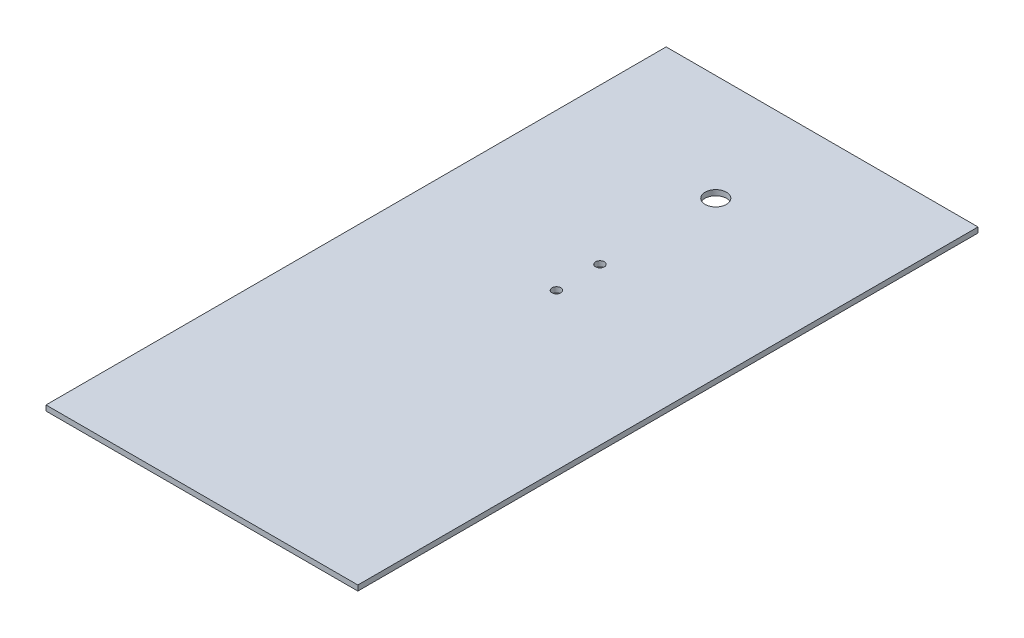
SolidWorks part; units mm, degrees
ref_plane "Front Plane" through (0, 0, 0) normal (0, 0, 1) x (1, 0, 0)
ref_plane "Top Plane" through (0, 0, 0) normal (0, 1, 0) x (1, 0, 0)
ref_plane "Right Plane" through (0, 0, 0) normal (1, 0, 0) x (0, 0, -1)
sketch "Sketch1" plane through (0, 0, 0) normal (0, 1, 0) x (1, 0, 0)
  line L1 (0, 0) -> (176, 0)
  line L2 (0, 0) -> (0, 350)
  line L3 (0, 350) -> (176, 350)
  line L4 (176, 0) -> (176, 350)
  dimension "D1" = 350
  dimension "D2" = 176
extrude "Boss-Extrude1" add sketch "Sketch1" along normal blind 3
hole_wizard "Ø5.0mm Dowel Hole1" positions "Sketch2" profile "Sketch3" hole size "Ø5.0" standard "ANSI Metric" end condition up to next
sketch "Sketch2" plane through (0, 0, 0) normal (0, -1, 0) x (-1, 0, 0)
  point P3 (-88.0169, 200.06)
  point P8 (-87.5916, 225.06)
sketch "Sketch3" plane through (88.0169, 0, -200.06) normal (1, 0, 0) x (0, 0, -1)
  line L0 (0, 0) -> (0, 3)
  line L1 (0, 3) -> (2.5, 3)
  line L2 (2.5, 3) -> (2.5, 0)
  line L5 (2.5, 0) -> (0, 0)
  line L11 (0, -6.35) -> (0, 107.95) construction
  dimension "Thru Hole Dia." = 5
  dimension "Thru Hole Depth" = 3
hole_wizard "Ø12.0mm Dowel Hole1" positions "Sketch6" profile "Sketch7" hole size "Ø12.0" standard "ANSI Metric" end condition up to next
sketch "Sketch6" plane through (0, 0, 0) normal (0, -1, 0) x (-1, 0, 0)
  point P0 (-88, 290)
sketch "Sketch7" plane through (88, 0, -290) normal (1, 0, 0) x (0, 0, -1)
  line L0 (0, 0) -> (0, 3)
  line L1 (0, 3) -> (6, 3)
  line L2 (6, 3) -> (6, 0)
  line L5 (6, 0) -> (0, 0)
  line L11 (0, -6.35) -> (0, 107.95) construction
  dimension "Thru Hole Dia." = 12
  dimension "Thru Hole Depth" = 3
sketch "Sketch10" plane through (0, 0, 0) normal (0, -1, 0) x (-1, 0, 0)
  line L0 (0, 0) -> (0, 175)
  line L1 (0, 350) -> (0, 0) construction
  line L2 (0, 175) -> (-88, 175)
sketch "Sketch12" plane through (0, 0, 0) normal (0, -1, 0) x (1, 0, 0)
  line L0 (125.0175, -130.5545) -> (137.3405, -148.3212)
  line L1 (137.3405, -148.3212) -> (125.0175, -166.0877)
  line L2 (125.0175, -166.0877) -> (112.6944, -183.8543)
  line L3 (112.6944, -183.8543) -> (89.345, -183.8589)
  line L4 (89.345, -183.8589) -> (65.9955, -183.8635)
  line L5 (65.9955, -183.8635) -> (65.9955, -187.2421)
  line L6 (65.9955, -187.2421) -> (65.9955, -190.6207)
  line L7 (65.9955, -190.6207) -> (66.5384, -190.9684)
  line L8 (62.6707, -191.0073) -> (63.1648, -190.6986)
  line L9 (63.1648, -190.6986) -> (63.169, -187.1666)
  line L10 (63.169, -187.1666) -> (63.1733, -183.6346)
  line L11 (63.1733, -183.6346) -> (50.9163, -165.9779)
  line L12 (50.9163, -165.9779) -> (38.6593, -148.3212)
  line L13 (38.6593, -148.3212) -> (50.9824, -130.5546)
  line L14 (50.9824, -130.5546) -> (63.3055, -112.788)
  line L15 (63.3055, -112.788) -> (88, -112.788)
  line L16 (88, -112.788) -> (112.6944, -112.788)
  line L17 (112.6944, -112.788) -> (125.0175, -130.5545)
  line L18 (58.6619, -161.6826) -> (67.9075, -175)
  line L19 (67.9075, -175) -> (88, -175)
  line L20 (88, -175) -> (108.0925, -175)
  line L21 (108.0925, -175) -> (117.3386, -161.6826)
  line L22 (108.8404, -122.7226) -> (108.0527, -121.5979)
  line L23 (108.0527, -121.5979) -> (87.9801, -121.6201)
  line L24 (87.9801, -121.6201) -> (67.9074, -121.6424)
  line L25 (67.9074, -121.6424) -> (58.6617, -134.9597)
  line L26 (70.518, -199.3662) -> (71.2886, -200.1403)
  line L27 (71.2886, -200.1403) -> (70.7807, -200.5699)
  line L28 (59.0664, -199.3966) -> (59.8103, -198.6687)
  line L29 (59.8103, -198.6687) -> (60.2791, -199.0503)
  line L30 (74.7643, -203.6125) -> (75.534, -204.3858)
  line L31 (75.534, -204.3858) -> (74.976, -204.8921)
  line L32 (54.138, -204.6844) -> (53.9663, -204.4929)
  line L33 (53.9663, -204.4929) -> (54.729, -203.7303)
  line L34 (54.729, -203.7303) -> (55.4916, -202.9677)
  line L35 (55.4916, -202.9677) -> (56.0106, -203.4191)
  line L36 (73.2802, -203.4581) -> (73.9945, -202.8392)
  line L37 (73.9945, -202.8392) -> (74.7643, -203.6125)
  line L38 (78.6937, -207.5419) -> (79.4376, -208.2897)
  line L39 (79.4376, -208.2897) -> (79.1768, -208.5656)
  line L40 (50.1699, -208.6539) -> (49.9988, -208.463)
  line L41 (49.9988, -208.463) -> (50.7412, -207.7168)
  spline S0 degree 3 poles (66.5384, -190.9684) (67.521, -191.5975) (68.2003, -192.821) (68.2003, -193.9618) knots 0 0 0 0 1 1 1 1
  spline S1 degree 3 poles (68.2003, -193.9618) (68.2003, -196.2879) (65.8545, -198.0438) (63.6438, -197.3723) knots 0 0 0 0 1 1 1 1
  spline S2 degree 3 poles (63.6438, -197.3723) (62.1379, -196.9149) (61.0566, -195.4901) (61.0566, -193.9632) knots 0 0 0 0 1 1 1 1
  spline S3 degree 3 poles (61.0566, -193.9632) (61.0566, -192.8424) (61.7418, -191.5877) (62.6707, -191.0073) knots 0 0 0 0 1 1 1 1
  spline S4 degree 3 poles (58.6617, -134.9597) (53.5766, -142.2843) (49.416, -148.2969) (49.4161, -148.3212) knots 0 0 0 0 1 1 1 1
  spline S5 degree 3 poles (49.4161, -148.3212) (49.4161, -148.3454) (53.5767, -154.3581) (58.6619, -161.6826) knots 0 0 0 0 1 1 1 1
  spline S6 degree 3 poles (117.3386, -161.6826) (122.424, -154.3581) (126.5696, -148.3243) (126.551, -148.2743) knots 0 0 0 0 1 1 1 1
  spline S7 degree 3 poles (126.551, -148.2743) (126.5225, -148.1976) (111.2429, -126.1533) (108.8404, -122.7226) knots 0 0 0 0 1 1 1 1
  spline S8 degree 3 poles (104.4924, -139.9991) (106.428, -140.3056) (107.9222, -141.0342) (109.2403, -142.3143) knots 0 0 0 0 1 1 1 1
  spline S9 degree 3 poles (109.2403, -142.3143) (110.3763, -143.4176) (111.1423, -144.744) (111.5224, -146.2661) knots 0 0 0 0 1 1 1 1
  spline S10 degree 3 poles (111.5224, -146.2661) (111.7959, -147.3613) (111.7959, -149.1047) (111.5224, -150.1998) knots 0 0 0 0 1 1 1 1
  spline S11 degree 3 poles (111.5224, -150.1998) (111.1567, -151.6643) (110.4704, -152.8897) (109.3968, -153.9952) knots 0 0 0 0 1 1 1 1
  spline S12 degree 3 poles (109.3968, -153.9952) (108.2935, -155.1312) (106.9671, -155.8972) (105.445, -156.2773) knots 0 0 0 0 1 1 1 1
  spline S13 degree 3 poles (105.445, -156.2773) (104.8373, -156.4291) (104.4103, -156.4711) (103.4781, -156.4711) knots 0 0 0 0 1 1 1 1
  spline S14 degree 3 poles (103.4781, -156.4711) (102.546, -156.4711) (102.119, -156.4291) (101.5113, -156.2773) knots 0 0 0 0 1 1 1 1
  spline S15 degree 3 poles (101.5113, -156.2773) (99.9726, -155.8931) (98.6337, -155.1148) (97.5379, -153.9678) knots 0 0 0 0 1 1 1 1
  spline S16 degree 3 poles (97.5379, -153.9678) (96.4551, -152.8345) (95.7978, -151.6574) (95.4338, -150.1998) knots 0 0 0 0 1 1 1 1
  spline S17 degree 3 poles (95.4338, -150.1998) (95.1603, -149.1047) (95.1603, -147.3613) (95.4338, -146.2661) knots 0 0 0 0 1 1 1 1
  spline S18 degree 3 poles (95.4338, -146.2661) (95.8139, -144.744) (96.5799, -143.4176) (97.7159, -142.3143) knots 0 0 0 0 1 1 1 1
  spline S19 degree 3 poles (97.7159, -142.3143) (99.2694, -140.8057) (101.0325, -140.0602) (103.2135, -139.9899) knots 0 0 0 0 1 1 1 1
  spline S20 degree 3 poles (103.2135, -139.9899) (103.7714, -139.9719) (104.3468, -139.976) (104.4924, -139.9991) knots 0 0 0 0 1 1 1 1
  spline S21 degree 3 poles (73.6243, -139.9991) (75.56, -140.3056) (77.0541, -141.0342) (78.3722, -142.3143) knots 0 0 0 0 1 1 1 1
  spline S22 degree 3 poles (78.3722, -142.3143) (79.5083, -143.4176) (80.2743, -144.744) (80.6544, -146.2661) knots 0 0 0 0 1 1 1 1
  spline S23 degree 3 poles (80.6544, -146.2661) (80.9279, -147.3613) (80.9279, -149.1047) (80.6544, -150.1998) knots 0 0 0 0 1 1 1 1
  spline S24 degree 3 poles (80.6544, -150.1998) (80.2887, -151.6643) (79.6024, -152.8897) (78.5287, -153.9952) knots 0 0 0 0 1 1 1 1
  spline S25 degree 3 poles (78.5287, -153.9952) (77.4254, -155.1312) (76.0991, -155.8972) (74.5769, -156.2773) knots 0 0 0 0 1 1 1 1
  spline S26 degree 3 poles (74.5769, -156.2773) (73.9692, -156.4291) (73.5422, -156.4711) (72.6101, -156.4711) knots 0 0 0 0 1 1 1 1
  spline S27 degree 3 poles (72.6101, -156.4711) (71.6779, -156.4711) (71.2509, -156.4291) (70.6432, -156.2773) knots 0 0 0 0 1 1 1 1
  spline S28 degree 3 poles (70.6432, -156.2773) (69.1046, -155.8931) (67.7657, -155.1148) (66.6698, -153.9678) knots 0 0 0 0 1 1 1 1
  spline S29 degree 3 poles (66.6698, -153.9678) (65.5871, -152.8345) (64.9298, -151.6574) (64.5658, -150.1998) knots 0 0 0 0 1 1 1 1
  spline S30 degree 3 poles (64.5658, -150.1998) (64.2922, -149.1047) (64.2922, -147.3613) (64.5658, -146.2661) knots 0 0 0 0 1 1 1 1
  spline S31 degree 3 poles (64.5658, -146.2661) (64.9459, -144.744) (65.7118, -143.4176) (66.8479, -142.3143) knots 0 0 0 0 1 1 1 1
  spline S32 degree 3 poles (66.8479, -142.3143) (68.4013, -140.8057) (70.1645, -140.0602) (72.3455, -139.9899) knots 0 0 0 0 1 1 1 1
  spline S33 degree 3 poles (72.3455, -139.9899) (72.9033, -139.9719) (73.4788, -139.976) (73.6243, -139.9991) knots 0 0 0 0 1 1 1 1
  spline S34 degree 3 poles (70.7807, -200.5699) (69.7071, -201.478) (68.385, -202.1628) (66.9838, -202.5367) knots 0 0 0 0 1 1 1 1
  spline S35 degree 3 poles (66.9838, -202.5367) (66.2322, -202.7372) (65.9557, -202.7651) (64.7167, -202.7651) knots 0 0 0 0 1 1 1 1
  spline S36 degree 3 poles (64.7167, -202.7651) (63.4777, -202.7651) (63.2011, -202.7372) (62.4496, -202.5367) knots 0 0 0 0 1 1 1 1
  spline S37 degree 3 poles (62.4496, -202.5367) (61.4451, -202.2687) (60.3126, -201.7572) (59.4858, -201.1981) knots 0 0 0 0 1 1 1 1
  spline S38 degree 3 poles (59.4858, -201.1981) (58.8495, -200.7678) (58.3226, -200.3145) (58.3226, -200.1973) knots 0 0 0 0 1 1 1 1
  spline S39 degree 3 poles (58.3226, -200.1973) (58.3226, -200.1572) (58.6573, -199.7969) (59.0664, -199.3966) knots 0 0 0 0 1 1 1 1
  spline S40 degree 3 poles (60.2791, -199.0503) (62.8797, -201.1669) (66.8079, -201.1224) (69.2776, -198.9485) knots 0 0 0 0 1 1 1 1
  spline S41 degree 3 poles (69.2776, -198.9485) (69.5004, -198.7524) (69.6972, -198.592) (69.715, -198.592) knots 0 0 0 0 1 1 1 1
  spline S42 degree 3 poles (69.715, -198.592) (69.7328, -198.592) (70.0942, -198.9404) (70.518, -199.3662) knots 0 0 0 0 1 1 1 1
  spline S43 degree 3 poles (74.976, -204.8921) (72.5058, -207.1332) (69.5802, -208.4453) (66.216, -208.8207) knots 0 0 0 0 1 1 1 1
  spline S44 degree 3 poles (66.216, -208.8207) (62.2649, -209.2616) (58.1263, -208.0026) (54.9364, -205.3892) knots 0 0 0 0 1 1 1 1
  spline S45 degree 3 poles (54.9364, -205.3892) (54.5917, -205.1069) (54.2325, -204.7897) (54.138, -204.6844) knots 0 0 0 0 1 1 1 1
  spline S46 degree 3 poles (56.0106, -203.4191) (57.3137, -204.5524) (59.0064, -205.5328) (60.5274, -206.0351) knots 0 0 0 0 1 1 1 1
  spline S47 degree 3 poles (60.5274, -206.0351) (61.9657, -206.51) (62.9154, -206.6512) (64.6726, -206.6512) knots 0 0 0 0 1 1 1 1
  spline S48 degree 3 poles (64.6726, -206.6512) (66.0329, -206.6512) (66.4581, -206.6181) (67.2302, -206.4523) knots 0 0 0 0 1 1 1 1
  spline S49 degree 3 poles (67.2302, -206.4523) (69.5899, -205.9457) (71.501, -204.9999) (73.2802, -203.4581) knots 0 0 0 0 1 1 1 1
  spline S50 degree 3 poles (79.1768, -208.5656) (79.0333, -208.7174) (78.5389, -209.1586) (78.0781, -209.546) knots 0 0 0 0 1 1 1 1
  spline S51 degree 3 poles (78.0781, -209.546) (74.3623, -212.6703) (69.4527, -214.4664) (64.6285, -214.4664) knots 0 0 0 0 1 1 1 1
  spline S52 degree 3 poles (64.6285, -214.4664) (59.8054, -214.4664) (54.9066, -212.6748) (51.1788, -209.5476) knots 0 0 0 0 1 1 1 1
  spline S53 degree 3 poles (51.1788, -209.5476) (50.718, -209.1611) (50.264, -208.7589) (50.1699, -208.6539) knots 0 0 0 0 1 1 1 1
  spline S54 degree 3 poles (50.7412, -207.7168) (51.1495, -207.3063) (51.5043, -206.9719) (51.5296, -206.9736) knots 0 0 0 0 1 1 1 1
  spline S55 degree 3 poles (51.5296, -206.9736) (51.555, -206.9753) (51.9862, -207.3309) (52.4878, -207.7637) knots 0 0 0 0 1 1 1 1
  spline S56 degree 3 poles (52.4878, -207.7637) (56.8268, -211.5071) (62.6098, -213.0196) (68.2885, -211.8962) knots 0 0 0 0 1 1 1 1
  spline S57 degree 3 poles (68.2885, -211.8962) (71.5103, -211.2589) (74.3225, -209.8757) (76.8924, -207.6644) knots 0 0 0 0 1 1 1 1
  spline S58 degree 3 poles (76.8924, -207.6644) (77.4487, -207.1857) (77.9141, -206.7941) (77.9268, -206.7941) knots 0 0 0 0 1 1 1 1
  spline S59 degree 3 poles (77.9268, -206.7941) (77.9394, -206.7941) (78.2845, -207.1306) (78.6937, -207.5419) knots 0 0 0 0 1 1 1 1
extrude "Cut-Extrude3" cut sketch "Sketch12" against normal blind 0.5 contours S59 S58 S57 S56 S55 S54 L41 L40 S53 S52 S51 S50 L39 L38 | S42 S41 S40 L29 L28 S39 S38 S37 S36 S35 S34 L27 L26 | S3 S2 S1 S0 L7 L6 L5 L4 L3 L2 L1 L0 L17 L16 L15 L14 L13 L12 L11 L10 L9 L8 S7 S6 L21 L20 L19 L18 S5 S4 L25 L24 L23 L22 | S20 S19 S18 S17 S16 S15 S14 S13 S12 S11 S10 S9 S8 | S33 S32 S31 S30 S29 S28 S27 S26 S25 S24 S23 S22 S21 | S47 S48 S49 L36 L37 L30 L31 S43 S44 S45 L32 L33 L34 L35 S46
